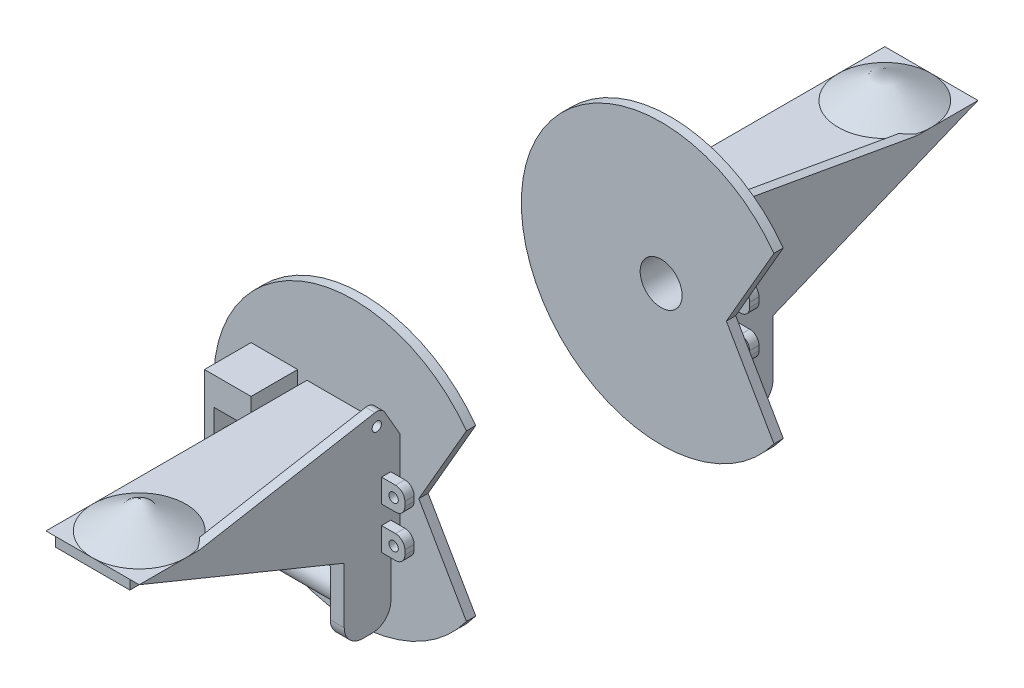
SolidWorks part; units mm, degrees
ref_plane "Płaszczyzna przednia" through (0, 0, 0) normal (0, 0, 1) x (1, 0, 0)
ref_plane "Płaszczyzna górna" through (0, 0, 0) normal (0, 1, 0) x (1, 0, 0)
ref_plane "Płaszczyzna prawa" through (0, 0, 0) normal (1, 0, 0) x (0, 0, -1)
sketch "Szkic1" plane through (0, 0, 0) normal (0, 0, 1) x (1, 0, 0)
  line L1 (-50, 50) -> (50, 50)
  line L2 (-50, 50) -> (-50, -50)
  line L3 (-50, -50) -> (50, -50)
  line L4 (50, 50) -> (50, -50)
  line L5 (-50, 50) -> (50, -50) construction
  line L6 (-50, -50) -> (50, 50) construction
  point P0 (0, 0)
  dimension "D1" = 100
extrude "Dodanie-wyciągnięcie1" add sketch "Szkic1" along normal blind 40
sketch "Szkic3" plane through (0, 0, 40) normal (0, 0, 1) x (1, 0, 0)
  circle A0 centre (0, 0) radius 22.5
  dimension "D1" = 45
extrude "Wytnij-wyciągnięcie1" cut sketch "Szkic3" against normal through all
sketch "Szkic4" plane through (0, 0, 0) normal (0, 0, -1) x (-1, 0, 0)
  line L0 (50, 50) -> (50, -50) construction
  line L1 (-50, -50) -> (50, -50)
  line L2 (-50, -50) -> (-50, -40)
  line L3 (-50, -40) -> (50, -40)
  line L4 (50, -50) -> (50, -40)
  dimension "D1" = 10
extrude "Dodanie-wyciągnięcie2" add sketch "Szkic4" along normal blind 30
sketch "Szkic5" plane through (-50, 0, 0) normal (-1, 0, 0) x (0, 0, 1)
  line L0 (-30, -40) -> (-250, 50)
  line L1 (-250, 50) -> (0, 50)
  line L2 (-30, -40) -> (0, -40) construction
  line L3 (0, 50) -> (0, -40) construction
  line L4 (-30, -40) -> (0, -40)
  line L5 (0, 50) -> (0, -40)
  dimension "D1" = 250
extrude "Dodanie-wyciągnięcie3" add sketch "Szkic5" against normal blind 10 contours L0 L1 L5 L4
sketch "Szkic6" plane through (50, 0, 0) normal (1, 0, 0) x (0, 0, -1)
  line L10 (30, -40) -> (250, 50)
  line L11 (250, 50) -> (0, 50)
  line L12 (0, 50) -> (0, -40)
  line L13 (0, -40) -> (30, -40)
  line L14 (30, -40) -> (250, 50)
  line L15 (250, 50) -> (0, 50)
  line L16 (0, 50) -> (0, -40)
  line L17 (0, -40) -> (30, -40)
  dimension "D1" = 0
extrude "Dodanie-wyciągnięcie4" add sketch "Szkic6" against normal blind 10
sketch "Szkic7" plane through (0, 50, 0) normal (0, 1, 0) x (1, 0, 0)
  line L0 (-40, 250) -> (40, 250)
  line L1 (-40, 250) -> (-40, 0) construction
  line L2 (-40, 30) -> (-40, 0) construction
  line L3 (40, 0) -> (-40, 0) construction
  line L5 (-40, 250) -> (-40, 0)
  line L6 (-40, 30) -> (-40, 0)
  line L7 (40, 0) -> (-40, 0)
  line L8 (40, 250) -> (40, 0) construction
  line L9 (40, 250) -> (40, 0)
extrude "Dodanie-wyciągnięcie5" add sketch "Szkic7" against normal blind 10
ref_plane "Płaszczyzna1" through (0, 0, -200) normal (0, 0, -1) x (-1, 0, 0)
sketch "Szkic10" plane through (0, 0, -200) normal (0, 0, -1) x (-1, 0, 0)
  line L0 (0, 50) -> (0, 80)
  line L1 (40, 50) -> (-40, 50) construction
  line L2 (0, 80) -> (-50, 50)
  line L3 (-50, 50) -> (0, 50)
  dimension "D1" = 30
revolve "Obrót1" add sketch "Szkic10" angle 360 about L0
sketch "Szkic11" plane through (0, -50, 0) normal (0, -1, 0) x (1, 0, 0)
  line L5 (50, 40) -> (50, -30) construction
  line L6 (50, 20) -> (35, 20)
  line L7 (50, 20) -> (50, -30)
  line L8 (50, -30) -> (35, -30)
  line L9 (35, 20) -> (35, -30)
  line L10 (50, -30) -> (-50, -30) construction
  dimension "D1" = 50
  dimension "D2" = 15
extrude "Dodanie-wyciągnięcie6" add sketch "Szkic11" along normal blind 70
sketch "Szkic12" plane through (35, 0, 0) normal (-1, 0, 0) x (0, 0, 1)
  line L0 (20, -120) -> (-30, -120) construction
  line L1 (20, -120) -> (20, -50) construction
  circle A0 centre (-5, -85) radius 15
  dimension "D1" = 30
  dimension "D2" = 35
  dimension "D3" = 25
extrude "Dodanie-wyciągnięcie7" add sketch "Szkic12" along normal blind 125
sketch "Szkic13" plane through (-50, 0, 0) normal (-1, 0, 0) x (0, 0, 1)
  circle A0 centre (-40, 0) radius 15
  dimension "D1" = 30
  dimension "D2" = 40
extrude "Dodanie-wyciągnięcie8" add sketch "Szkic13" along normal blind 30
ref_plane "Płaszczyzna2" through (-60, 0, 0) normal (-1, 0, 0) x (0, 0, 1)
sketch "Szkic14" plane through (-60, 0, 0) normal (-1, 0, 0) x (0, 0, 1)
  line L0 (20, -120) -> (-30, -120) construction
  line L1 (-69.0109, 20.0371) -> (-26.9998, 36.1636)
  line L2 (-69.0109, 20.0371) -> (-15.2557, -120)
  line L3 (-15.2557, -120) -> (26.7554, -103.8734)
  line L4 (-26.9998, 36.1636) -> (26.7554, -103.8734)
  line L5 (-30, -120) -> (-30, -50) construction
  circle A3 centre (-5, -85) radius 15 construction
  dimension "D2" = 159
  dimension "D4" = 29
  dimension "D1" = 150
  dimension "D3" = 45
extrude "Dodanie-wyciągnięcie9" add sketch "Szkic14" along normal blind 10
fillet "Zaokrąglenie1" radius 20 6 edges at (42.5, -120, 20) (42.5, -120, -30) (-65, 36.1636, -26.9998) (-65, 20.0371, -69.0109) (-65, -103.8734, 26.7554) (-65, -120, -15.2557)
sketch "Szkic15" plane through (-90, 0, 0) normal (-1, 0, 0) x (0, 0, 1)
  line L0 (0, -120) -> (-10, -120) construction
  line L1 (-30, 65) -> (20, 65)
  line L2 (-30, 65) -> (-30, -120)
  line L3 (-30, -120) -> (20, -120)
  line L4 (20, 65) -> (20, -120)
  line L5 (20, -100) -> (20, -50) construction
  line L6 (-30, -100) -> (-30, -50) construction
  dimension "D1" = 185
sketch "Szkic17" plane through (-50, 0, 0) normal (-1, 0, 0) x (0, 0, 1)
  line L0 (-30, 65) -> (-30, -120) construction
  line L1 (-30, 65) -> (20, 65)
  line L2 (-30, 65) -> (-30, 35)
  line L3 (-30, 35) -> (20, 35)
  line L4 (20, 65) -> (20, 35)
  line L6 (20, 65) -> (20, -120) construction
  line L9 (-30, 65) -> (20, 65) construction
  dimension "D1" = 30
extrude "Dodanie-wyciągnięcie10" add sketch "Szkic15" along normal blind 10 contours L1 L4 L3 L2
extrude "Dodanie-wyciągnięcie11" add sketch "Szkic17" along normal up to next contours L1 L4 L3 L2
sketch "Szkic18" plane through (0, 0, 40) normal (0, 0, 1) x (1, 0, 0)
  line L0 (121.1021, 88.5115) -> (70, 0)
  line L1 (70, 0) -> (121.1021, -88.5115)
  line L2 (50, -50) -> (50, 50) construction
  circle A0 centre (0, 0) radius 150
  line M4 (50, -50) -> (50, 50)
  line M5 (50, 50) -> (-50, 50)
  line M6 (-50, 50) -> (-50, -50)
  line M7 (-50, -50) -> (50, -50)
  dimension "D1" = 300
  dimension "D2" = 70
  dimension "D3" = 120
  dimension "D4" = 30
extrude "Dodanie-wyciągnięcie12" add sketch "Szkic18" against normal blind 10 contours L0 A0 L1 M4 M7 M6 M5
sketch "Szkic19" plane through (50, 0, 0) normal (1, 0, 0) x (0, 0, -1)
  line L0 (-30, 50) -> (-9.9586, 84.6171)
  line L1 (-9.9586, 84.6171) -> (185, 50)
  line L2 (-30, 50) -> (200, 50) construction
  line L3 (185, 50) -> (-30, 50)
  dimension "D1" = 65
  dimension "D2" = 40
  dimension "D3" = 110
extrude "Dodanie-wyciągnięcie13" add sketch "Szkic19" against normal blind 10 contours L1 L3 L0
sketch "Szkic20" plane through (50, 0, 0) normal (1, 0, 0) x (0, 0, -1)
  circle A0 centre (-4.9586, 69.6171) radius 5
  dimension "D1" = 10
  dimension "D2" = 15
  dimension "D3" = 5
extrude "Wytnij-wyciągnięcie2" cut sketch "Szkic20" against normal up to next
sketch "Szkic21" plane through (50, 0, 0) normal (1, 0, 0) x (0, 0, -1)
  line L1 (-20, -50) -> (-10, -50)
  line L2 (-20, -50) -> (-20, 20)
  line L3 (-20, 20) -> (-10, 20)
  line L4 (-10, -50) -> (-10, 20)
  line L5 (-20, -5) -> (-10, -5)
  line L6 (-20, -5) -> (-20, -25)
  line L7 (-20, -25) -> (-10, -25)
  line L8 (-10, -5) -> (-10, -25)
  point P9 (-15, -50)
  dimension "D1" = 70
  dimension "D2" = 10
  dimension "D3" = 25
  dimension "D4" = 25
extrude "Dodanie-wyciągnięcie14" add sketch "Szkic21" along normal blind 25 contours L2 L5 L4 L3 | L7 L2 L1 L4
fillet "Zaokrąglenie2" radius 10 5 edges at (75, -50, 15) (75, -25, 15) (75, -5, 15) (75, 20, 15) (45, 84.6171, 9.9586)
sketch "Szkic22" plane through (0, 0, 10) normal (0, 0, -1) x (-1, 0, 0)
  line L0 (-75, 5) -> (-75, 10) construction
  circle A0 centre (-63, 7.5) radius 5
  circle A1 centre (-63, -37.5) radius 5
  dimension "D1" = 12
  dimension "D2" = 10
  dimension "D4" = 10
  dimension "D3" = 2.5
  dimension "D5" = 2.5
extrude "Wytnij-wyciągnięcie3" cut sketch "Szkic22" against normal up to next
ref_plane "Płaszczyzna3" through (0, 0, 200) normal (0, 0, 1) x (1, 0, 0)
mirror "Lustro2" about plane through (0, 0, 200) normal (0, 0, 1) of bodies 118
